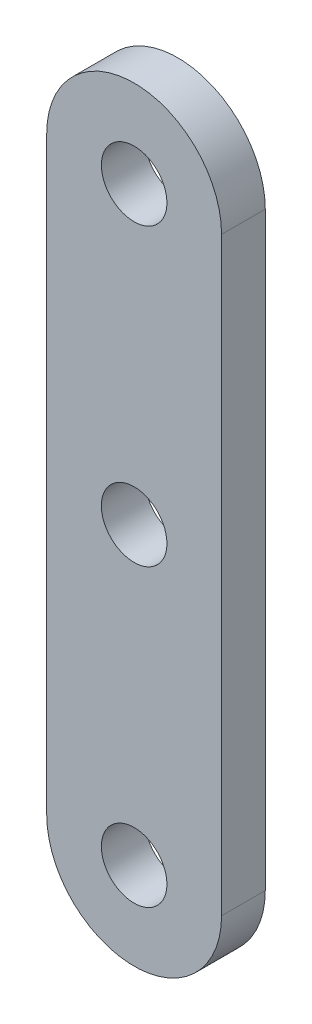
SolidWorks part; units mm, degrees
ref_plane "Front Plane" through (0, 0, 0) normal (0, 0, 1) x (1, 0, 0)
ref_plane "Top Plane" through (0, 0, 0) normal (0, 1, 0) x (1, 0, 0)
ref_plane "Right Plane" through (0, 0, 0) normal (1, 0, 0) x (0, 0, -1)
sketch "Sketch1" plane through (0, 0, 0) normal (0, 0, 1) x (1, 0, 0)
  line L0 (0, 2.3813) -> (0, 40.4813)
  line L1 (0, 0) -> (0, 42.8625) construction
  line L2 (-6.35, 0) -> (-6.35, 42.8625)
  line L3 (6.35, 0) -> (6.35, 42.8625)
  circle A0 centre (0, 0) radius 2.3813
  circle A1 centre (0, 42.8625) radius 2.3812
  circle A2 centre (0, 21.4312) radius 2.3813
  arc A3 (-6.35, 0) -> (6.35, 0) centre (0, 0) ccw
  arc A4 (6.35, 42.8625) -> (-6.35, 42.8625) centre (0, 42.8625) ccw
  point P9 (0, 21.4313)
  dimension "D1" = 4.7625
  dimension "D2" = 4.7625
  dimension "D4" = 4.7625
  dimension "D5" = 6.35
  dimension "D3" = 38.1
extrude "Boss-Extrude1" add sketch "Sketch1" along normal blind 3.175
